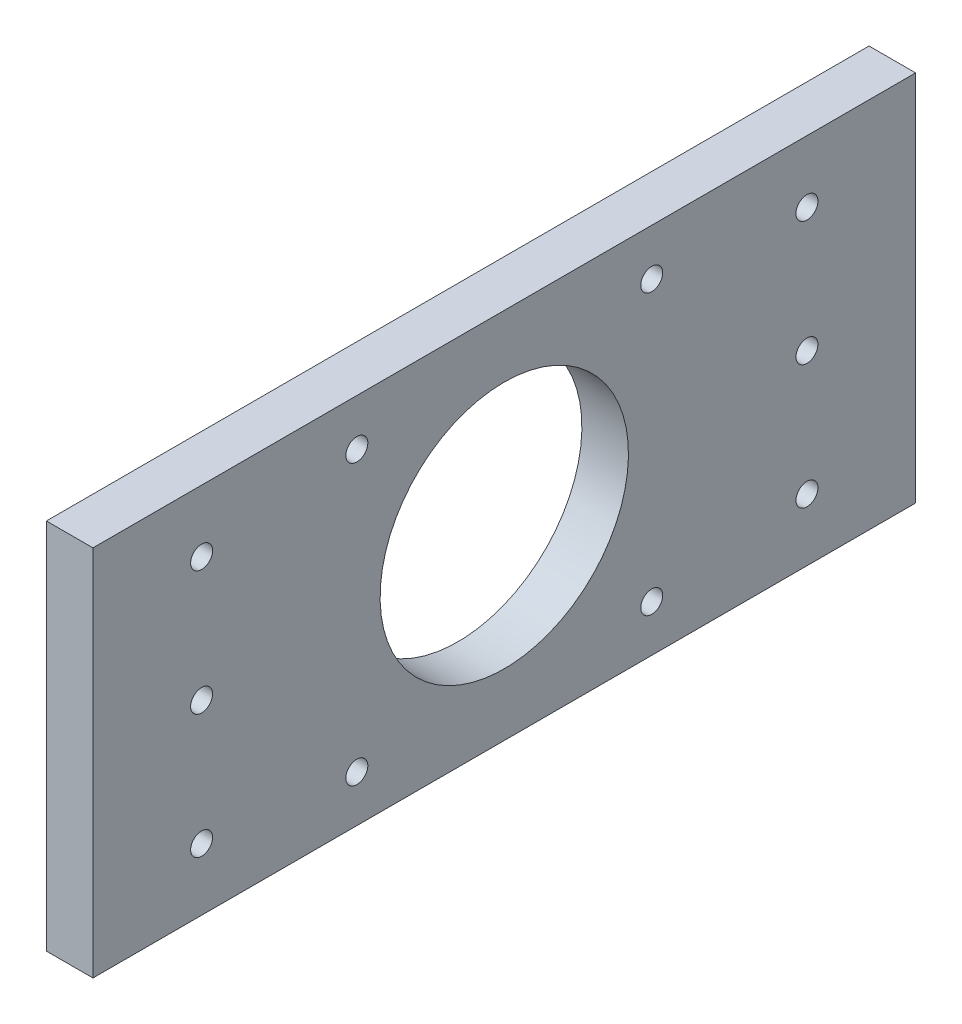
SolidWorks part; units mm, degrees
material "AISI 1015 Steel, Cold Drawn (SS)"
ref_plane "Front Plane" through (0, 0, 0) normal (0, 0, 1) x (1, 0, 0)
ref_plane "Top Plane" through (0, 0, 0) normal (0, 1, 0) x (1, 0, 0)
ref_plane "Right Plane" through (0, 0, 0) normal (1, 0, 0) x (0, 0, -1)
sketch "Sketch1" plane through (0, 0, 0) normal (0, 0, 1) x (1, 0, 0)
  line L1 (-4.7625, 38.1) -> (4.7625, 38.1)
  line L2 (-4.7625, 38.1) -> (-4.7625, -38.1)
  line L3 (-4.7625, -38.1) -> (4.7625, -38.1)
  line L4 (4.7625, 38.1) -> (4.7625, -38.1)
  line L5 (-4.7625, 38.1) -> (4.7625, -38.1) construction
  line L6 (-4.7625, -38.1) -> (4.7625, 38.1) construction
  point P0 (0, 0)
  dimension "D1" = 9.525
  dimension "D2" = 76.2
extrude "Boss-Extrude1" add sketch "Sketch1" along normal blind 168.275
hole_wizard "#8 Clearance Hole1" positions "Sketch3" profile "Sketch2" hole size "#8" standard "ANSI Inch" end condition through all
sketch "Sketch3" plane through (4.7625, 0, 0) normal (1, 0, 0) x (0, 0, -1)
  line L0 (-168.275, -38.1) -> (0, -38.1) construction
  line L1 (-168.275, -38.1) -> (-168.275, 38.1) construction
  line L2 (0, -38.1) -> (0, 38.1) construction
  point P0 (-146.05, 25.4)
  point P2 (-146.05, 0)
  point P4 (-146.05, -25.4)
  point P6 (-22.225, 25.4)
  point P8 (-22.225, 0)
  point P10 (-22.225, -25.4)
  point P17 (-168.275, 0)
  dimension "D1" = 25.4
  dimension "D2" = 25.4
  dimension "D3" = 12.7
  dimension "D4" = 22.225
  dimension "D5" = 22.225
sketch "Sketch2" plane through (4.7625, 25.4, 146.05) normal (0, 1, 0) x (0, 0, -1)
  line L0 (0, 0) -> (0, 9.525)
  line L1 (0, 9.525) -> (2.2479, 9.525)
  line L2 (2.2479, 9.525) -> (2.2479, 0)
  line L5 (2.2479, 0) -> (0, 0)
  line L11 (0, -6.35) -> (0, 107.95) construction
  dimension "Thru Hole Dia." = 4.4958
  dimension "Thru Hole Depth" = 9.525
hole_wizard "#8 Clearance Hole2" positions "Sketch4" profile "Sketch5" hole size "#8" standard "ANSI Inch" end condition through all
sketch "Sketch4" plane through (4.7625, 0, 0) normal (1, 0, 0) x (0, 0, -1)
  line L0 (-168.275, 38.1) -> (-114.3, 28.575) construction
  line L2 (-114.3, -28.575) -> (-168.275, -38.1) construction
  line L5 (-53.975, -28.575) -> (0, -38.1) construction
  line L8 (-53.975, 28.575) -> (0, 38.1) construction
  point P0 (-114.3, 28.575)
  point P2 (-53.975, 28.575)
  point P4 (-53.975, -28.575)
  point P6 (-114.3, -28.575)
  dimension "D1" = 60.325
  dimension "D2" = 57.15
sketch "Sketch5" plane through (4.7625, 28.575, 114.3) normal (0, 1, 0) x (0, 0, -1)
  line L0 (0, 0) -> (0, 9.525)
  line L1 (0, 9.525) -> (2.2479, 9.525)
  line L2 (2.2479, 9.525) -> (2.2479, 0)
  line L5 (2.2479, 0) -> (0, 0)
  line L11 (0, -6.35) -> (0, 107.95) construction
  dimension "Thru Hole Dia." = 4.4958
  dimension "Thru Hole Depth" = 9.525
sketch "Sketch6" plane through (4.7625, 0, 0) normal (1, 0, 0) x (0, 0, -1)
  line L0 (0, -38.1) -> (0, 38.1) construction
  line L1 (-168.275, -38.1) -> (-84.1375, 0) construction
  line L2 (-84.1375, 0) -> (0, -38.1) construction
  circle A0 centre (-84.1375, 0) radius 25.4
  point P5 (0, 0)
  dimension "D1" = 50.8
extrude "Cut-Extrude1" cut sketch "Sketch6" against normal through all
